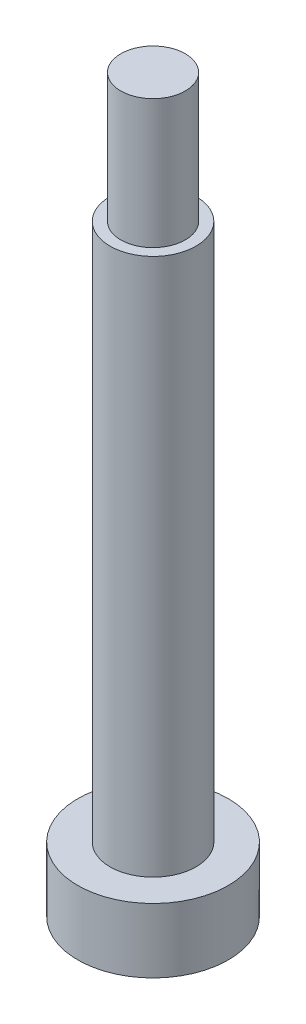
SolidWorks part; units mm, degrees
material "304不锈钢"
ref_plane "前视基准面" through (0, 0, 0) normal (0, 0, 1) x (1, 0, 0)
ref_plane "上视基准面" through (0, 0, 0) normal (0, 1, 0) x (1, 0, 0)
ref_plane "右视基准面" through (0, 0, 0) normal (1, 0, 0) x (0, 0, -1)
sketch "草图1" plane through (0, 0, 0) normal (0, 1, 0) x (1, 0, 0)
  circle A0 centre (0, 0) radius 2
  dimension "D1" = 4
extrude "凸台-拉伸1" add sketch "草图1" along normal blind 25
sketch "草图2" plane through (0, 25, 0) normal (0, 1, 0) x (1, 0, 0)
  circle A0 centre (0, 0) radius 1.5
  dimension "D1" = 3
extrude "凸台-拉伸2" add sketch "草图2" along normal blind 6
cosmetic thread "装饰螺纹线1" parameters "D2"=2.459
sketch "草图3" plane through (0, 0, 0) normal (0, -1, 0) x (1, 0, 0)
  circle A0 centre (0, 0) radius 3.5
  dimension "D1" = 7
extrude "凸台-拉伸3" add sketch "草图3" along normal blind 3
